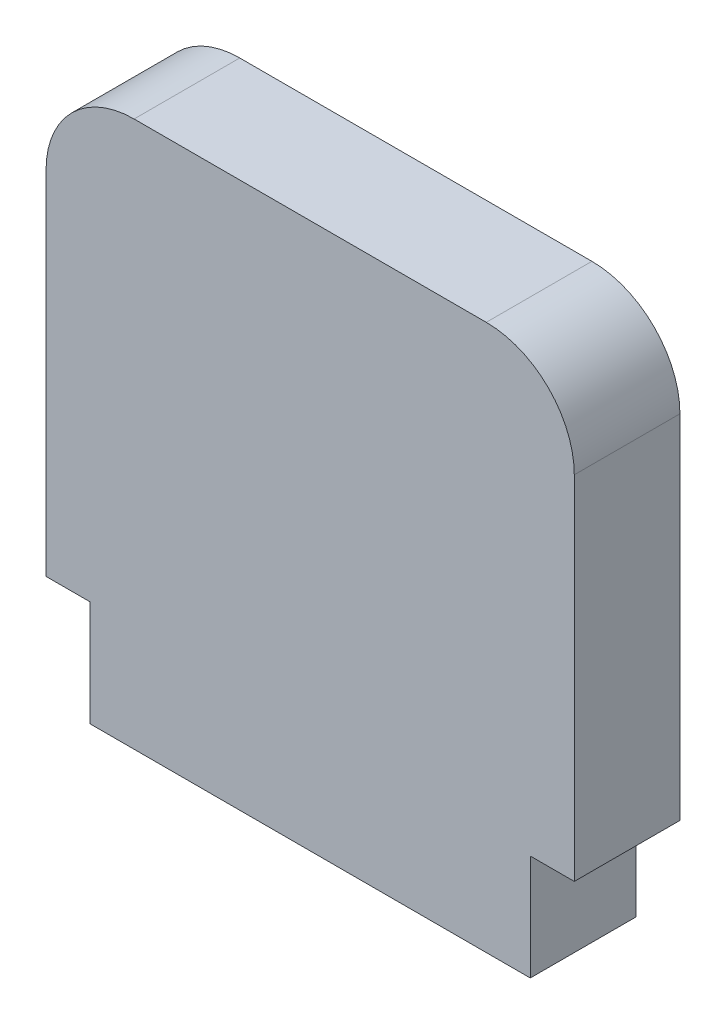
SolidWorks part; units mm, degrees
material "MDF"
ref_plane "Plano frontal" through (0, 0, 0) normal (0, 0, 1) x (1, 0, 0)
ref_plane "Plano superior" through (0, 0, 0) normal (0, 1, 0) x (1, 0, 0)
ref_plane "Plano direito" through (0, 0, 0) normal (1, 0, 0) x (0, 0, -1)
sketch "Esboço1" plane through (0, 0, 0) normal (0, 0, 1) x (1, 0, 0)
  line L1 (-15, -12.5) -> (15, -12.5)
  line L2 (-15, -12.5) -> (-15, 12.5)
  line L3 (-15, 12.5) -> (15, 12.5)
  line L4 (15, -12.5) -> (15, 12.5)
  line L5 (0, 12.5) -> (0, -12.5) construction
  line L6 (-15, 0) -> (15, 0) construction
  line L7 (12.5, -18.5) -> (-12.5, -18.5)
  line L8 (12.5, -18.5) -> (12.5, -12.5)
  line L9 (12.5, -12.5) -> (-12.5, -12.5)
  line L10 (-12.5, -18.5) -> (-12.5, -12.5)
  line L11 (0, -12.5) -> (0, -18.5) construction
  line L12 (12.5, -15.5) -> (-12.5, -15.5) construction
  point P0 (0, 0)
  point P4 (0, -15.5)
  dimension "D1" = 6
  dimension "D2" = 25
  dimension "D3" = 30
  dimension "D4" = 25
extrude "Ressalto-extrusão1" add sketch "Esboço1" along normal blind 6 contours L1 L4 L3 L2 | L10 L7 L8 L1
fillet "Filete1" radius 5 2 edges at (15, 12.5, 3) (-15, 12.5, 3)
